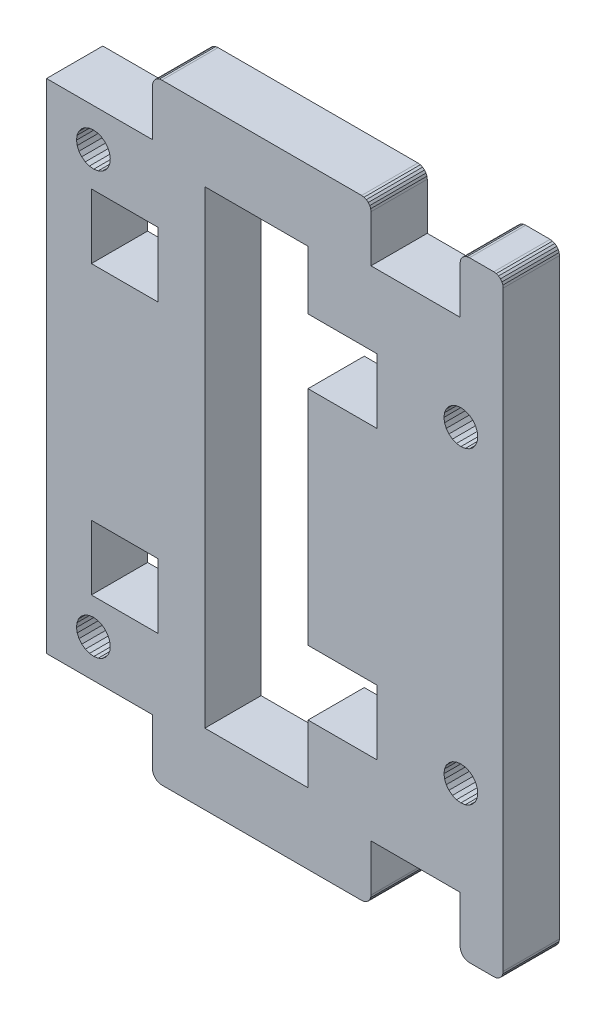
SolidWorks part; units mm, degrees
material "Maple"
ref_plane "Front Plane" through (0, 0, 0) normal (0, 0, 1) x (1, 0, 0)
ref_plane "Top Plane" through (0, 0, 0) normal (0, 1, 0) x (1, 0, 0)
ref_plane "Right Plane" through (0, 0, 0) normal (1, 0, 0) x (0, 0, -1)
sketch "Sketch1" plane through (0, 0, 0) normal (0, 0, 1) x (1, 0, 0)
  line L1570 (-357.6109, -342.3726) -> (-357.6723, -342.8385)
  line L1571 (-397.0584, -347.4826) -> (-396.8674, -347.9119)
  line L1572 (-397.354, -347.1173) -> (-397.0584, -347.4826)
  line L1573 (-399.1041, -346.6965) -> (-398.64, -346.6232)
  line L1574 (-400.3436, -348.0018) -> (-400.175, -347.5632)
  line L1575 (-400.3195, -348.9332) -> (-400.3929, -348.4691)
  line L1576 (-399.8329, -349.7278) -> (-400.1285, -349.3626)
  line L1577 (-358.9949, -293.5066) -> (-358.7537, -293.4067)
  line L1578 (-369.2864, -293.6655) -> (-369.4935, -293.5066)
  line L1579 (-369.4935, -293.5066) -> (-369.7346, -293.4067)
  line L1580 (-358.1381, -341.0998) -> (-357.8521, -341.4726)
  line L1581 (-360.6837, -343.6454) -> (-360.9698, -343.2726)
  line L1582 (-359.8768, -344.1113) -> (-360.3109, -343.9314)
  line L1583 (-357.8521, -343.2726) -> (-358.1381, -343.6454)
  line L1584 (-398.8109, -307.1726) -> (-391.7109, -307.1726)
  line L1585 (-375.7109, -337.7726) -> (-368.3425, -337.7726)
  line L1586 (-360.9698, -343.2726) -> (-361.1496, -342.8385)
  line L1587 (-360.6837, -341.0998) -> (-360.3109, -340.8137)
  line L1588 (-397.2882, -349.6621) -> (-397.6535, -349.9577)
  line L1589 (-361.1496, -341.9067) -> (-360.9698, -341.4726)
  line L1590 (-358.1381, -310.7454) -> (-358.5109, -311.0314)
  line L1591 (-369.2864, -358.1797) -> (-369.4935, -358.3386)
  line L1592 (-359.202, -293.6655) -> (-358.9949, -293.5066)
  line L1593 (-391.5523, -293.4067) -> (-391.2935, -293.3726)
  line L1594 (-392.2594, -357.7314) -> (-392.1595, -357.9726)
  line L1595 (-375.7109, -350.9226) -> (-375.7109, -344.6726)
  line L1596 (-375.7109, -337.7726) -> (-375.7109, -314.0726)
  line L1597 (-375.7109, -307.1726) -> (-368.3425, -307.1726)
  line L1598 (-398.8109, -314.0726) -> (-398.8109, -307.1726)
  line L1599 (-368.9935, -357.4726) -> (-368.9935, -352.4726)
  line L1600 (-355.6404, -358.4385) -> (-355.8991, -358.4726)
  line L1601 (-369.0275, -357.7314) -> (-369.1274, -357.9726)
  line L1602 (-369.1274, -357.9726) -> (-369.2864, -358.1797)
  line L1603 (-368.3425, -344.6726) -> (-375.7109, -344.6726)
  line L1604 (-391.7109, -314.0726) -> (-398.8109, -314.0726)
  line L1605 (-386.7109, -350.9226) -> (-375.7109, -350.9226)
  line L1606 (-392.2935, -352.4726) -> (-392.2935, -357.4726)
  line L1607 (-355.1881, -293.6655) -> (-355.0292, -293.8726)
  line L1608 (-355.0292, -293.8726) -> (-354.9293, -294.1138)
  line L1609 (-359.4949, -294.3726) -> (-359.4949, -299.3726)
  line L1610 (-354.9293, -294.1138) -> (-354.8952, -294.3726)
  line L1611 (-359.4949, -294.3726) -> (-359.4608, -294.1138)
  line L1612 (-359.4608, -294.1138) -> (-359.3609, -293.8726)
  line L1613 (-400.3212, -303.9275) -> (-400.393, -303.4632)
  line L1614 (-400.1316, -304.3575) -> (-400.3212, -303.9275)
  line L1615 (-368.9935, -299.3726) -> (-368.9935, -294.3726)
  line L1616 (-354.8991, -357.4734) -> (-354.9334, -357.732)
  line L1617 (-354.9334, -357.732) -> (-355.0334, -357.973)
  line L1618 (-355.0334, -357.973) -> (-355.1923, -358.18)
  line L1619 (-361.1496, -309.0067) -> (-360.9698, -308.5726)
  line L1620 (-357.6723, -341.9067) -> (-357.6109, -342.3726)
  line L1621 (-398.64, -346.6232) -> (-398.1727, -346.6725)
  line L1622 (-399.5334, -346.8875) -> (-399.1041, -346.6965)
  line L1623 (-392.1595, -357.9726) -> (-392.0006, -358.1797)
  line L1624 (-392.0006, -358.1797) -> (-391.7935, -358.3386)
  line L1625 (-391.7935, -358.3386) -> (-391.5523, -358.4385)
  line L1626 (-391.2935, -358.4726) -> (-369.9935, -358.4726)
  line L1627 (-391.5523, -358.4385) -> (-391.2935, -358.4726)
  line L1628 (-355.8952, -293.3726) -> (-358.4949, -293.3726)
  line L1629 (-368.3425, -314.0726) -> (-375.7109, -314.0726)
  line L1630 (-400.175, -347.5632) -> (-399.8987, -347.1831)
  line L1631 (-400.3929, -348.4691) -> (-400.3436, -348.0018)
  line L1632 (-358.9935, -358.3386) -> (-358.7523, -358.4385)
  line L1633 (-358.4935, -358.4726) -> (-355.8991, -358.4726)
  line L1634 (-358.7523, -358.4385) -> (-358.4935, -358.4726)
  line L1635 (-368.9935, -294.3726) -> (-369.0275, -294.1138)
  line L1636 (-369.0275, -294.1138) -> (-369.1274, -293.8726)
  line L1637 (-369.1274, -293.8726) -> (-369.2864, -293.6655)
  line L1638 (-392.2935, -357.4726) -> (-392.2594, -357.7314)
  line L1639 (-392.2935, -294.3726) -> (-392.2594, -294.1138)
  line L1640 (-392.2594, -294.1138) -> (-392.1595, -293.8726)
  line L1641 (-392.1595, -293.8726) -> (-392.0006, -293.6655)
  line L1642 (-392.0006, -293.6655) -> (-391.7935, -293.5066)
  line L1643 (-391.7935, -293.5066) -> (-391.5523, -293.4067)
  line L1644 (-357.6723, -342.8385) -> (-357.8521, -343.2726)
  line L1645 (-358.7537, -293.4067) -> (-358.4949, -293.3726)
  line L1646 (-399.8372, -304.7238) -> (-400.1316, -304.3575)
  line L1647 (-399.4581, -305.0013) -> (-399.8372, -304.7238)
  line L1648 (-399.02, -305.1713) -> (-399.4581, -305.0013)
  line L1649 (-398.5529, -305.2221) -> (-399.02, -305.1713)
  line L1650 (-369.4935, -358.3386) -> (-369.7346, -358.4385)
  line L1651 (-369.7346, -358.4385) -> (-369.9935, -358.4726)
  line L1652 (-359.4935, -357.4726) -> (-359.4594, -357.7314)
  line L1653 (-359.4594, -357.7314) -> (-359.3595, -357.9726)
  line L1654 (-359.3595, -357.9726) -> (-359.2006, -358.1797)
  line L1655 (-359.2006, -358.1797) -> (-358.9935, -358.3386)
  line L1656 (-369.9935, -293.3726) -> (-391.2935, -293.3726)
  line L1657 (-369.7346, -293.4067) -> (-369.9935, -293.3726)
  line L1658 (-397.6535, -349.9577) -> (-398.0828, -350.1486)
  line L1659 (-397.0119, -349.282) -> (-397.2882, -349.6621)
  line L1660 (-396.8433, -348.8434) -> (-397.0119, -349.282)
  line L1661 (-396.7941, -348.3761) -> (-396.8433, -348.8434)
  line L1662 (-396.8674, -347.9119) -> (-396.7941, -348.3761)
  line L1663 (-357.8521, -308.5726) -> (-357.6723, -309.0067)
  line L1664 (-358.1381, -308.1998) -> (-357.8521, -308.5726)
  line L1665 (-360.3109, -340.8137) -> (-359.8768, -340.6339)
  line L1666 (-361.1496, -342.8385) -> (-361.2109, -342.3726)
  line L1667 (-359.3609, -293.8726) -> (-359.202, -293.6655)
  line L1668 (-355.8952, -293.3726) -> (-355.6364, -293.4067)
  line L1669 (-355.6364, -293.4067) -> (-355.3952, -293.5066)
  line L1670 (-355.3952, -293.5066) -> (-355.1881, -293.6655)
  line L1671 (-403.5935, -299.3726) -> (-392.2935, -299.3726)
  line L1672 (-386.7109, -300.9226) -> (-386.7109, -350.9226)
  line L1673 (-368.3425, -337.7726) -> (-368.3425, -344.6726)
  line L1674 (-391.7109, -344.6726) -> (-398.8109, -344.6726)
  line L1675 (-391.7109, -337.7726) -> (-391.7109, -344.6726)
  line L1676 (-358.5109, -340.8137) -> (-358.1381, -341.0998)
  line L1677 (-359.8768, -340.6339) -> (-359.4109, -340.5726)
  line L1678 (-398.8109, -337.7726) -> (-391.7109, -337.7726)
  line L1679 (-357.8521, -341.4726) -> (-357.6723, -341.9067)
  line L1680 (-358.945, -340.6339) -> (-358.5109, -340.8137)
  line L1681 (-359.4109, -340.5726) -> (-358.945, -340.6339)
  line L1682 (-361.2109, -309.4726) -> (-361.1496, -309.0067)
  line L1683 (-360.6837, -310.7454) -> (-360.9698, -310.3726)
  line L1684 (-355.1923, -358.18) -> (-355.3993, -358.3387)
  line L1685 (-355.3993, -358.3387) -> (-355.6404, -358.4385)
  line L1686 (-358.945, -344.1113) -> (-359.4109, -344.1726)
  line L1687 (-358.5109, -343.9314) -> (-358.945, -344.1113)
  line L1688 (-358.1381, -343.6454) -> (-358.5109, -343.9314)
  line L1689 (-361.2109, -342.3726) -> (-361.1496, -341.9067)
  line L1690 (-368.9935, -357.4726) -> (-369.0275, -357.7314)
  line L1691 (-403.5935, -299.3726) -> (-403.5935, -352.4726)
  line L1692 (-359.4949, -299.3726) -> (-368.9935, -299.3726)
  line L1693 (-360.9698, -308.5726) -> (-360.6837, -308.1998)
  line L1694 (-360.6837, -308.1998) -> (-360.3109, -307.9137)
  line L1695 (-398.8109, -344.6726) -> (-398.8109, -337.7726)
  line L1696 (-359.4935, -352.4726) -> (-368.9935, -352.4726)
  line L1697 (-403.5935, -352.4726) -> (-392.2935, -352.4726)
  line L1698 (-392.2935, -299.3726) -> (-392.2935, -294.3726)
  line L1699 (-400.1285, -349.3626) -> (-400.3195, -348.9332)
  line L1700 (-359.4935, -352.4726) -> (-359.4935, -357.4726)
  line L1701 (-360.3109, -343.9314) -> (-360.6837, -343.6454)
  line L1702 (-398.0885, -305.1503) -> (-398.5529, -305.2221)
  line L1703 (-397.6585, -304.9607) -> (-398.0885, -305.1503)
  line L1704 (-397.2923, -304.6664) -> (-397.6585, -304.9607)
  line L1705 (-397.0147, -304.2872) -> (-397.2923, -304.6664)
  line L1706 (-396.8447, -303.8491) -> (-397.0147, -304.2872)
  line L1707 (-396.7939, -303.382) -> (-396.8447, -303.8491)
  line L1708 (-396.8657, -302.9176) -> (-396.7939, -303.382)
  line L1709 (-397.0553, -302.4877) -> (-396.8657, -302.9176)
  line L1710 (-397.3497, -302.1214) -> (-397.0553, -302.4877)
  line L1711 (-397.7288, -301.8438) -> (-397.3497, -302.1214)
  line L1712 (-399.8987, -347.1831) -> (-399.5334, -346.8875)
  line L1713 (-358.5109, -307.9137) -> (-358.1381, -308.1998)
  line L1714 (-358.945, -307.7339) -> (-358.5109, -307.9137)
  line L1715 (-359.4109, -307.6726) -> (-358.945, -307.7339)
  line L1716 (-359.8768, -307.7339) -> (-359.4109, -307.6726)
  line L1717 (-360.3109, -307.9137) -> (-359.8768, -307.7339)
  line L1718 (-359.4109, -344.1726) -> (-359.8768, -344.1113)
  line L1719 (-360.3109, -311.0314) -> (-360.6837, -310.7454)
  line L1720 (-359.8768, -311.2113) -> (-360.3109, -311.0314)
  line L1721 (-359.4109, -311.2726) -> (-359.8768, -311.2113)
  line L1722 (-358.945, -311.2113) -> (-359.4109, -311.2726)
  line L1723 (-375.7109, -307.1726) -> (-375.7109, -300.9226)
  line L1724 (-375.7109, -300.9226) -> (-386.7109, -300.9226)
  line L1725 (-391.7109, -307.1726) -> (-391.7109, -314.0726)
  line L1726 (-368.3425, -307.1726) -> (-368.3425, -314.0726)
  line L1727 (-398.1727, -346.6725) -> (-397.734, -346.841)
  line L1728 (-397.734, -346.841) -> (-397.354, -347.1173)
  line L1729 (-360.9698, -310.3726) -> (-361.1496, -309.9385)
  line L1730 (-361.1496, -309.9385) -> (-361.2109, -309.4726)
  line L1731 (-360.9698, -341.4726) -> (-360.6837, -341.0998)
  line L1732 (-357.6723, -309.0067) -> (-357.6109, -309.4726)
  line L1733 (-398.0828, -350.1486) -> (-398.5469, -350.222)
  line L1734 (-398.5469, -350.222) -> (-399.0142, -350.1727)
  line L1735 (-399.0142, -350.1727) -> (-399.4529, -350.0042)
  line L1736 (-399.4529, -350.0042) -> (-399.8329, -349.7278)
  line L1737 (-357.6109, -309.4726) -> (-357.6723, -309.9385)
  line L1738 (-357.6723, -309.9385) -> (-357.8521, -310.3726)
  line L1739 (-357.8521, -310.3726) -> (-358.1381, -310.7454)
  line L1740 (-358.5109, -311.0314) -> (-358.945, -311.2113)
  line L1741 (-398.634, -301.623) -> (-398.1669, -301.6739)
  line L1742 (-398.1669, -301.6739) -> (-397.7288, -301.8438)
  line L1743 (-400.393, -303.4632) -> (-400.3422, -302.996)
  line L1744 (-400.3422, -302.996) -> (-400.1722, -302.558)
  line L1745 (-400.1722, -302.558) -> (-399.8946, -302.1788)
  line L1746 (-399.8946, -302.1788) -> (-399.5284, -301.8844)
  line L1747 (-399.5284, -301.8844) -> (-399.0984, -301.6949)
  line L1748 (-399.0984, -301.6949) -> (-398.634, -301.623)
  line L8367 (-354.8991, -357.4734) -> (-354.8952, -294.3726)
  line L8873 (-369.7583, -326.039) -> (-368.6781, -328.1929)
  line L8874 (-368.6781, -328.1929) -> (-369.7583, -326.039)
  line L8875 (-369.7583, -326.039) -> (-370.8385, -328.1929)
  line L8876 (-370.8385, -328.1929) -> (-369.7583, -326.039)
  line L8877 (-369.7583, -326.039) -> (-370.8385, -323.885)
  line L8878 (-370.8385, -323.885) -> (-369.7583, -326.039)
  line L8879 (-369.7583, -326.039) -> (-368.6781, -323.885)
  line L8880 (-368.6781, -323.885) -> (-369.7583, -326.039)
extrude "Boss-Extrude1" add sketch "Sketch1" along normal blind 6
